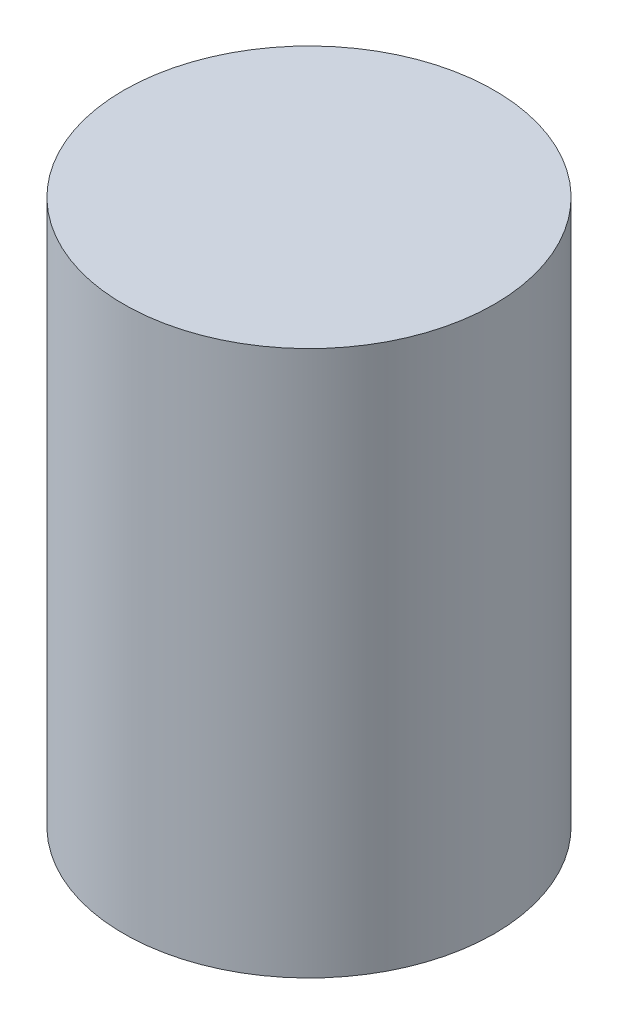
SolidWorks part; units mm, degrees
ref_plane "Front Plane" through (0, 0, 0) normal (0, 0, 1) x (1, 0, 0)
ref_plane "Top Plane" through (0, 0, 0) normal (0, 1, 0) x (1, 0, 0)
ref_plane "Right Plane" through (0, 0, 0) normal (1, 0, 0) x (0, 0, -1)
sketch "Sketch1" plane through (0, 0, 0) normal (0, 0, 1) x (1, 0, 0)
  line L0 (-7.5, -10) -> (-17, -10)
  line L1 (-17, -10) -> (-17, 40)
  line L2 (-17, 40) -> (0, 40)
  line L3 (0, 0) -> (0, 40) construction
  line L4 (0, 40) -> (0, 12.5)
  arc A0 (0, 12.5) -> (-7.5, -10) centre (0, 0) ccw
  dimension "D3" = 25
  dimension "D1" = 40
  dimension "D2" = 50
  dimension "D4" = 17
revolve "Revolve1" add sketch "Sketch1" angle 360 about L3
